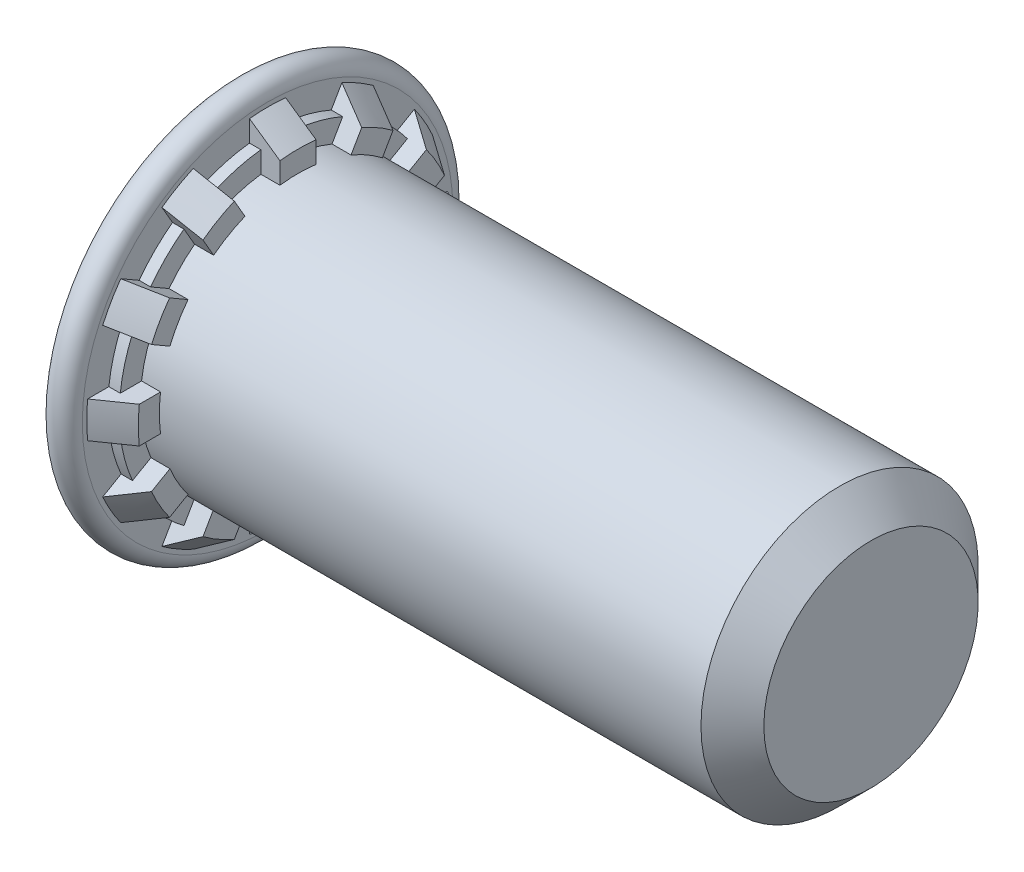
SolidWorks part; units mm, degrees
ref_plane "Plane1" through (0, 0, 0) normal (0, 0, 1) x (1, 0, 0)
ref_plane "Plane2" through (0, 0, 0) normal (0, 1, 0) x (1, 0, 0)
ref_plane "Plane3" through (0, 0, 0) normal (1, 0, 0) x (0, 0, -1)
sketch "BodySke" plane through (0, 0, 0) normal (0, 0, 1) x (1, 0, 0)
  line L0 (0, 0) -> (0, 2.7788)
  line L1 (0.4572, 2.7838) -> (0.4572, 2.7178)
  line L2 (0.4572, 2.7178) -> (0.9144, 2.4003)
  line L3 (0.9144, 2.0828) -> (9.0526, 2.0828)
  line L4 (9.525, 1.6104) -> (9.525, 0)
  line L5 (9.525, 0) -> (0, 0)
  line L6 (0, 0) -> (50.554, 0) construction
  line L7 (0.9144, 2.4003) -> (0.9144, 2.0828)
  line L8 (9.525, 1.6104) -> (9.0526, 2.0828)
  line L9 (-9.525, 3.0099) -> (9.525, 3.0099) construction
  line L11 (1.7069, 19.05) -> (1.7069, -3.175) construction
  line L13 (9.525, -3.0099) -> (-9.525, -3.0099) construction
  line L14 (0.0051, 2.7838) -> (0.0051, 2.7788)
  line L15 (0, 2.7788) -> (0.0051, 2.7788)
  arc A0 (0.0051, 2.7838) -> (0.4572, 2.7838) centre (0.2311, 2.7838) cw
  dimension "D2" = 0.0051
  dimension "D1" = 0.0051
  dimension "Diameter" = 4.1656
  dimension "Length" = 9.525
  dimension "Body_ch_ang" = 45
  dimension "Minor_dia" = 3.2207
  dimension "Advance" = 0.7925
  dimension "H_dia" = 6.0198
  dimension "Shoulder_lower_dia" = 5.4356
  dimension "Shoulder_upper_dia" = 4.8006
  dimension "Shoulder_ht" = 0.9144
  dimension "T_dim" = 0.4572
revolve "BaseBody" add sketch "BodySke" angle 360 about L6
cosmetic thread "ThreadCosmetic" [suppressed] parameters "Thread_length"=7.239, "Thread_minor"=3.2207
sketch "ThdSchSke" plane through (0, 0, 0) normal (0, 0, 1) x (1, 0, 0)
  line L0 (2.286, -1.6104) -> (1.9552, -2.0828)
  line L1 (2.286, -1.6104) -> (2.6168, -2.0828)
  line L2 (2.6168, -2.0828) -> (2.6168, -2.6035)
  line L3 (-3.175, 0) -> (5.1513, 0) construction
  line L5 (2.6168, -2.6035) -> (1.9552, -2.6035)
  line L6 (1.9552, -2.6035) -> (1.9552, -2.0828)
  line L7 (0, 2.7788) -> (0, -2.7788) construction
  dimension "Thread_minor" = 3.2207
  dimension "Diameter" = 4.1656
  dimension "Start" = 2.286
  dimension "SideAngle" = 55
  dimension "VeeAngle" = 70
  dimension "Overcut" = 5.207
revolve "ThreadSchematic" [suppressed] cut sketch "ThdSchSke" angle 360 about L3
pattern_linear "ThdSchPat" [suppressed]
sketch "RibCut1Ske" plane through (0.9144, 0, 0) normal (1, 0, 0) x (0, 0, -1)
  line L0 (0.2719, 2.065) -> (0.2719, 2.9976)
  line L1 (0.7971, 1.9243) -> (1.2634, 2.7319)
  line L2 (0, 0) -> (0, 4.9784) construction
  line L3 (0, 0) -> (0.2719, 2.065) construction
  line L4 (0, 0) -> (0.7971, 1.9243) construction
  arc A1 (0.7971, 1.9243) -> (0.2719, 2.065) centre (0, 0) ccw
  arc A2 (1.2634, 2.7319) -> (0.2719, 2.9976) centre (0, 0) ccw
  dimension "Inner_dia" = 4.1656
  dimension "Outer_dia" = 6.0198
  dimension "Rib_root_half_angle" = 7.5
  dimension "Rib_root_gap_angle" = 15
  dimension "Angle" = 30
extrude "RibCut1" cut sketch "RibCut1Ske" against normal blind 0.2858
sketch "RibCut2Ske" plane through (0.9144, 0, 0) normal (1, 0, 0) x (0, 0, -1)
  line L0 (0.2719, 2.3849) -> (0.2719, 2.9976)
  line L1 (0.957, 2.2013) -> (1.2634, 2.7319)
  line L2 (0.2719, 2.065) -> (0.2719, 3.8767) construction
  line L3 (0, 0) -> (0, 5.0239) construction
  line L4 (0, 0) -> (0.2719, 2.065) construction
  line L5 (0, 0) -> (0.7971, 1.9243) construction
  line L6 (0.7971, 1.9243) -> (1.7065, 3.4994) construction
  arc A1 (0.957, 2.2013) -> (0.2719, 2.3849) centre (0, 0) ccw
  arc A2 (1.2634, 2.7319) -> (0.2719, 2.9976) centre (0, 0) ccw
  circle A4 centre (0, 0) radius 2.0828 construction
  dimension "Inner_dia" = 4.8006
  dimension "Outer_dia" = 6.0198
  dimension "Rib_root_dia" = 4.1656
  dimension "Rib_root_half_angle" = 7.5
  dimension "Rib_root_gap_angle" = 15
  dimension "Angle" = 30
extrude "RibCut2" cut sketch "RibCut2Ske" against normal blind 0.4572
pattern_circular "RibCutsPat" count 12 every 30 about axis through (0, 0, 0) along (1, 0, 0) of "RibCut2", "RibCut1"
equation "' \"Length@BodySke\" = 0.75"
equation "' \"H_dia@BodySke\" = 0.337"
equation "' \"Start@ThdSchSke\" = 0.135"
equation "' \"Diameter@BodySke\" = 0.25"
equation "' \"Minor_dia@BodySke\" =0.1905"
equation "' \"Advance@BodySke\" = 0.05"
equation "\"T_dim@BodySke\" = \"Start@ThdSchSke\" * 0.2"
equation "\"Shoulder_ht@BodySke\" = \"Start@ThdSchSke\" * 0.4"
equation "\"Shoulder_lower_dia@BodySke\" = \"H_dia@BodySke\" - \"Start@ThdSchSke\" * 0.2 - .005"
equation "\"Shoulder_upper_dia@BodySke\" = ( \"Shoulder_lower_dia@BodySke\" + \"Diameter@BodySke\" ) /2"
equation "\"Num_ribs@RibCutsPat\" = 12"
equation "\"Angle@RibCutsPat\" = 360 / \"Num_ribs@RibCutsPat\""
equation "\"Angle@RibCut1Ske\" =\"Angle@RibCutsPat\""
equation "\"Rib_root_half_angle@RibCut1Ske\" = \"Angle@RibCut1Ske\" / 4"
equation "\"Rib_root_gap_angle@RibCut1Ske\" = \"Angle@RibCut1Ske\" - (2 * \"Rib_root_half_angle@RibCut1Ske\" )"
equation "\"Inner_dia@RibCut1Ske\" = \"Diameter@BodySke\""
equation "\"Outer_dia@RibCut1Ske\" = \"H_dia@BodySke\""
equation "\"Depth@RibCut1\" =  \"Start@ThdSchSke\" * 0.125"
equation "\"Angle@RibCut2Ske\" =\"Angle@RibCutsPat\""
equation "\"Rib_root_half_angle@RibCut2Ske\" = \"Angle@RibCut1Ske\" / 4"
equation "\"Rib_root_gap_angle@RibCut2Ske\" = \"Angle@RibCut1Ske\" - (2 * \"Rib_root_half_angle@RibCut1Ske\" )"
equation "\"Rib_root_dia@RibCut2Ske\" = \"Diameter@BodySke\""
equation "\"Inner_dia@RibCut2Ske\" = \"Shoulder_upper_dia@BodySke\""
equation "\"Outer_dia@RibCut2Ske\" = \"H_dia@BodySke\""
equation "\"Depth@RibCut2\" =  \"Start@ThdSchSke\" * 0.2"
equation "\"Thread_length@ThreadCosmetic\" = \"Length@BodySke\" - \"Start@ThdSchSke\""
equation "\"Thread_minor@ThreadCosmetic\" = \"Minor_dia@BodySke\""
equation "\"Thread_minor@ThdSchSke\" = \"Minor_dia@BodySke\""
equation "\"Diameter@ThdSchSke\" = \"Diameter@BodySke\""
equation "\"Overcut@ThdSchSke\" = \"Diameter@BodySke\" * 1.25"
equation "\"Num_threads@ThdSchPat\" = int( \"Thread_length@ThreadCosmetic\" / \"Advance@BodySke\" + 0.999 )  + 1"
equation "\"Advance@ThdSchPat\" = \"Thread_length@ThreadCosmetic\" /  (\"Num_threads@ThdSchPat\" - 1) 'relax it"
equation "\"Num_threads@ThdSchPat\" = \"Num_threads@ThdSchPat\" - sgn( \"Num_threads@ThdSchPat\" - 1) '---chamfered tips only---"
